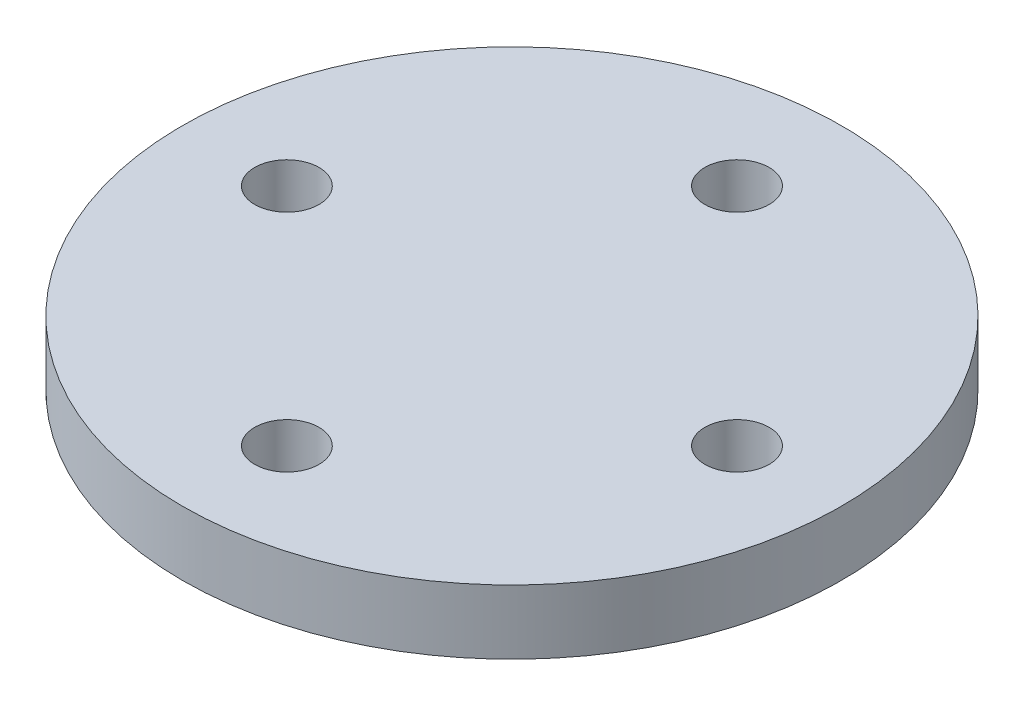
SolidWorks part; units mm, degrees
ref_plane "前视基准面" through (0, 0, 0) normal (0, 0, 1) x (1, 0, 0)
ref_plane "上视基准面" through (0, 0, 0) normal (0, 1, 0) x (1, 0, 0)
ref_plane "右视基准面" through (0, 0, 0) normal (1, 0, 0) x (0, 0, -1)
sketch "草图1" plane through (0, 0, 0) normal (0, 1, 0) x (1, 0, 0)
  circle A0 centre (0, 0) radius 10.25
  dimension "D1" = 20.5
extrude "凸台-拉伸1" add sketch "草图1" along normal blind 2
sketch "草图2" plane through (0, 0, 0) normal (0, -1, 0) x (1, 0, 0)
  circle A0 centre (0, 0) radius 4
  circle A1 centre (0, 0) radius 3
  dimension "D1" = 8
  dimension "D2" = 6
extrude "凸台-拉伸2" add sketch "草图2" along normal blind 3 contours A0 A1
sketch "草图4" plane through (0, 2, 0) normal (0, 1, 0) x (1, 0, 0)
  line L1 (-7, -7) -> (7, -7) construction
  line L2 (-7, -7) -> (-7, 7) construction
  line L3 (-7, 7) -> (7, 7) construction
  line L4 (7, -7) -> (7, 7) construction
  line L5 (-7, -7) -> (7, 7) construction
  line L6 (-7, 7) -> (7, -7) construction
  circle A0 centre (-7, 0) radius 1
  circle A1 centre (0, 7) radius 1
  circle A2 centre (7, 0) radius 1
  circle A5 centre (0, -7) radius 1
  point P0 (0, 0)
  dimension "D3" = 2
  dimension "D4" = 2
  dimension "D5" = 2
  dimension "D1" = 2
  dimension "D2" = 14
  dimension "D6" = 14
extrude "切除-拉伸1" cut sketch "草图4" against normal blind 3
